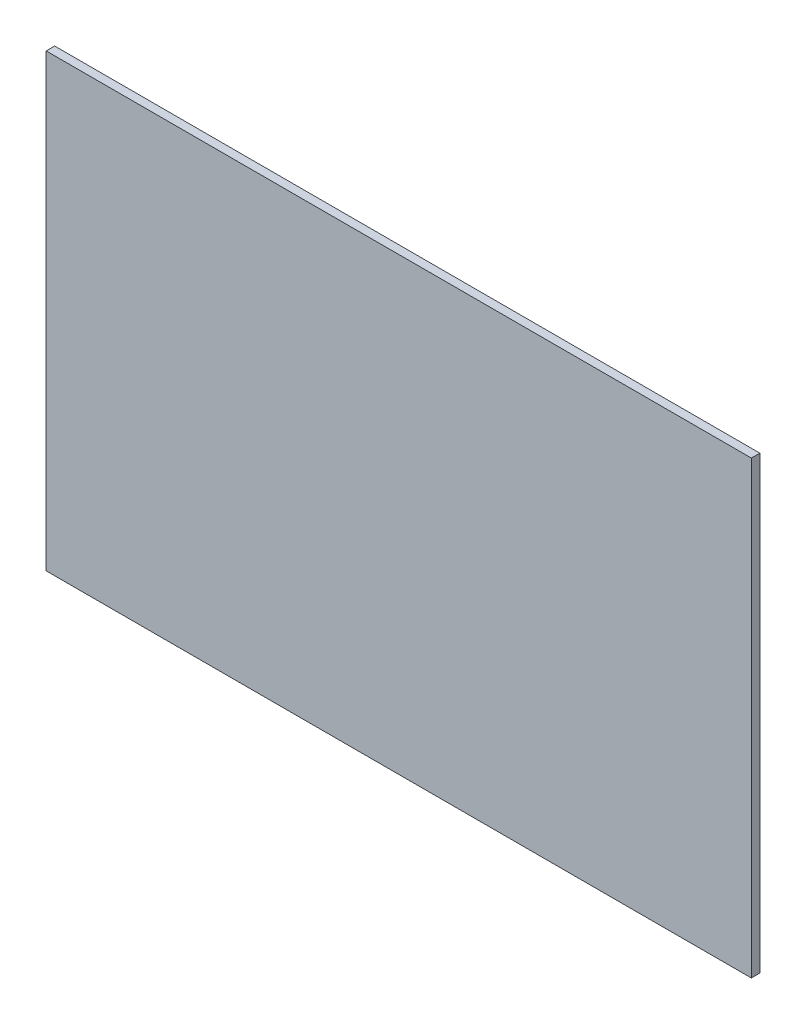
SolidWorks part; units mm, degrees
ref_plane "Front Plane" through (0, 0, 0) normal (0, 0, 1) x (1, 0, 0)
ref_plane "Top Plane" through (0, 0, 0) normal (0, 1, 0) x (1, 0, 0)
ref_plane "Right Plane" through (0, 0, 0) normal (1, 0, 0) x (0, 0, -1)
sketch "Sketch1" plane through (0, 0, 0) normal (0, 0, 1) x (1, 0, 0)
  line L1 (-83, -53) -> (83, -53)
  line L2 (-83, -53) -> (-83, 53)
  line L3 (-83, 53) -> (83, 53)
  line L4 (83, -53) -> (83, 53)
  line L5 (-83, -53) -> (83, 53) construction
  line L6 (-83, 53) -> (83, -53) construction
  point P0 (0, 0)
  dimension "D1" = 166
  dimension "06" = 106
extrude "DiffusePlate" add sketch "Sketch1" along normal blind 2
